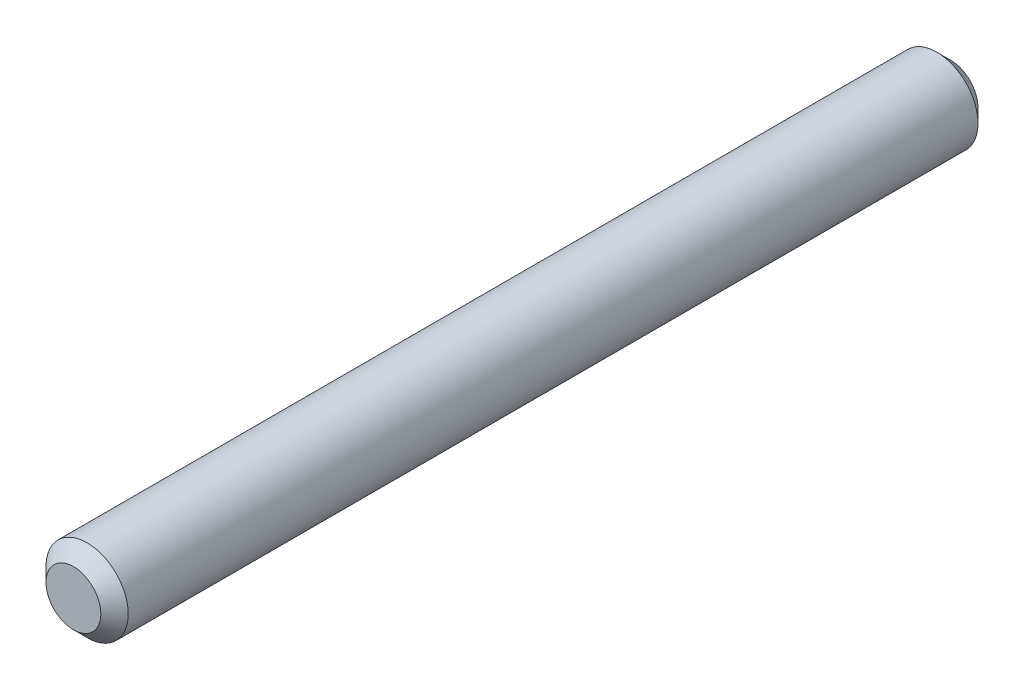
SolidWorks part; units mm, degrees
ref_plane "Front Plane" through (0, 0, 0) normal (0, 0, 1) x (1, 0, 0)
ref_plane "Top Plane" through (0, 0, 0) normal (0, 1, 0) x (1, 0, 0)
ref_plane "Right Plane" through (0, 0, 0) normal (1, 0, 0) x (0, 0, -1)
sketch "Sketch1" plane through (0, 0, 0) normal (0, 0, 1) x (1, 0, 0)
  circle A0 centre (0, 0) radius 0.75
  dimension "D1" = 1.5
extrude "Boss-Extrude1" add sketch "Sketch1" along normal blind 16
chamfer "Chamfer1" distance 0.25 angle 45 2 edges at (0.75, 0, 16) (0.75, 0, 0)
